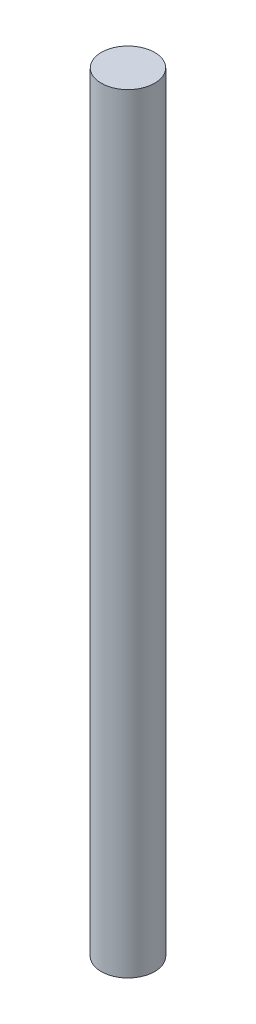
SolidWorks part; units mm, degrees
ref_plane "Front Plane" through (0, 0, 0) normal (0, 0, 1) x (1, 0, 0)
ref_plane "Top Plane" through (0, 0, 0) normal (0, 1, 0) x (1, 0, 0)
ref_plane "Right Plane" through (0, 0, 0) normal (1, 0, 0) x (0, 0, -1)
sketch "Sketch1" plane through (0, 0, 0) normal (0, 1, 0) x (1, 0, 0)
  circle A0 centre (0, 0) radius 1.5875
extrude "Boss-Extrude1" add sketch "Sketch1" along normal blind 45.72
equation "\"pegDiameter\"= .125"
equation "\"PegLength\"= 1.8"
equation "\"D1@Boss-Extrude1\" = \"PegLength\""
